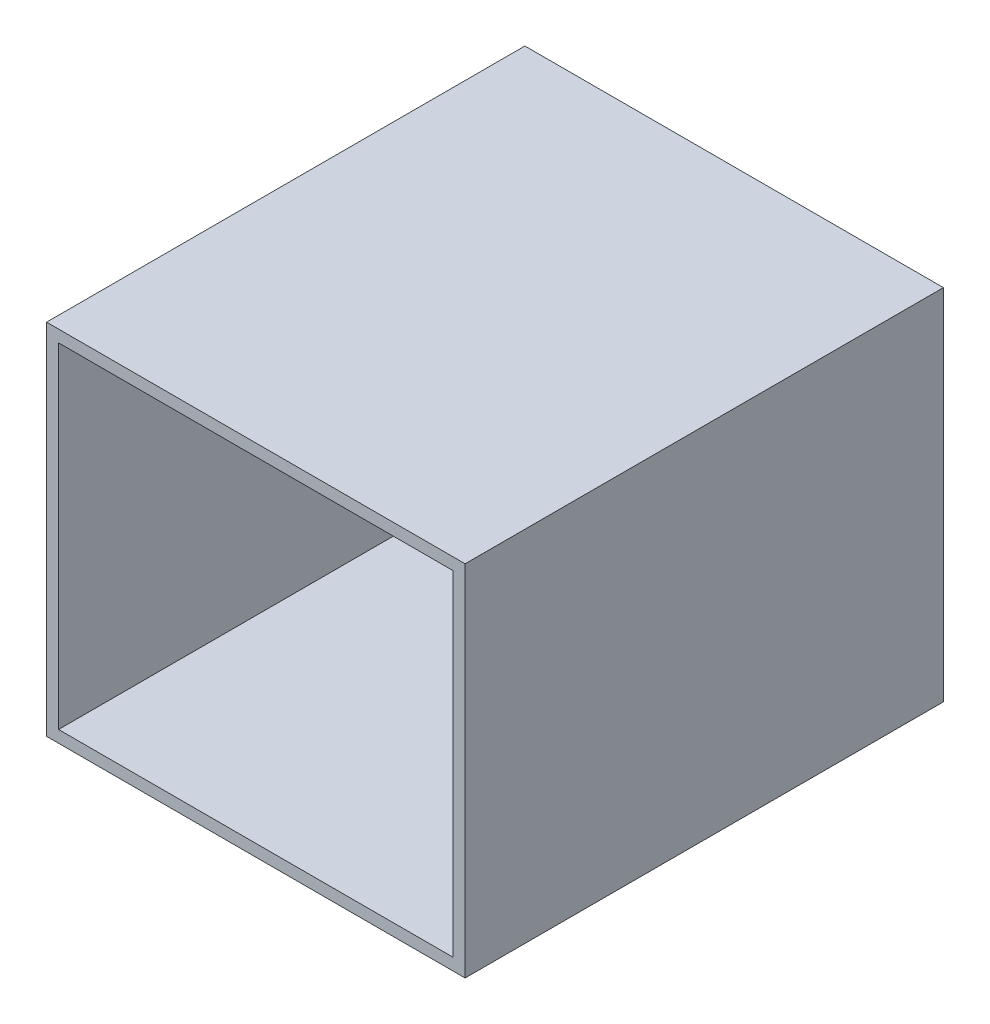
SolidWorks part; units mm, degrees
ref_plane "Front Plane" through (0, 0, 0) normal (0, 0, 1) x (1, 0, 0)
ref_plane "Top Plane" through (0, 0, 0) normal (0, 1, 0) x (1, 0, 0)
ref_plane "Right Plane" through (0, 0, 0) normal (1, 0, 0) x (0, 0, -1)
sketch "Sketch1" plane through (0, 0, 0) normal (0, 0, 1) x (1, 0, 0)
  line L0 (0, -34) -> (0, 34)
  line L1 (-175, 150) -> (175, 150)
  line L2 (-175, 150) -> (-175, -150)
  line L3 (-175, -150) -> (175, -150)
  line L4 (175, 150) -> (175, -150)
  line L5 (-34, 0) -> (34, 0)
  circle A0 centre (0, -2.864) radius 60
extrude "Boss-Extrude1" add sketch "Sketch1" along normal blind 10 contours L4 L1 L2 L3 A0
sketch "Sketch2" plane through (-175, 0, 0) normal (-1, 0, 0) x (0, 0, 1)
  line L1 (0, 150) -> (400, 150)
  line L2 (0, 150) -> (0, -150)
  line L3 (0, -150) -> (400, -150)
  line L4 (400, 150) -> (400, -150)
extrude "Boss-Extrude2" add sketch "Sketch2" against normal blind 10
mirror "Mirror1" about plane through (0, 0, 0) normal (1, 0, 0) of "Boss-Extrude2"
sketch "Sketch3" plane through (0, -150, 0) normal (0, -1, 0) x (1, 0, 0)
  line L1 (-175, 400) -> (175, 400)
  line L2 (-175, 400) -> (-175, 0)
  line L3 (-175, 0) -> (175, 0)
  line L4 (175, 400) -> (175, 0)
extrude "Boss-Extrude3" add sketch "Sketch3" against normal blind 10
mirror "Mirror2" about plane through (0, 0, 0) normal (0, 1, 0) of "Boss-Extrude3"
